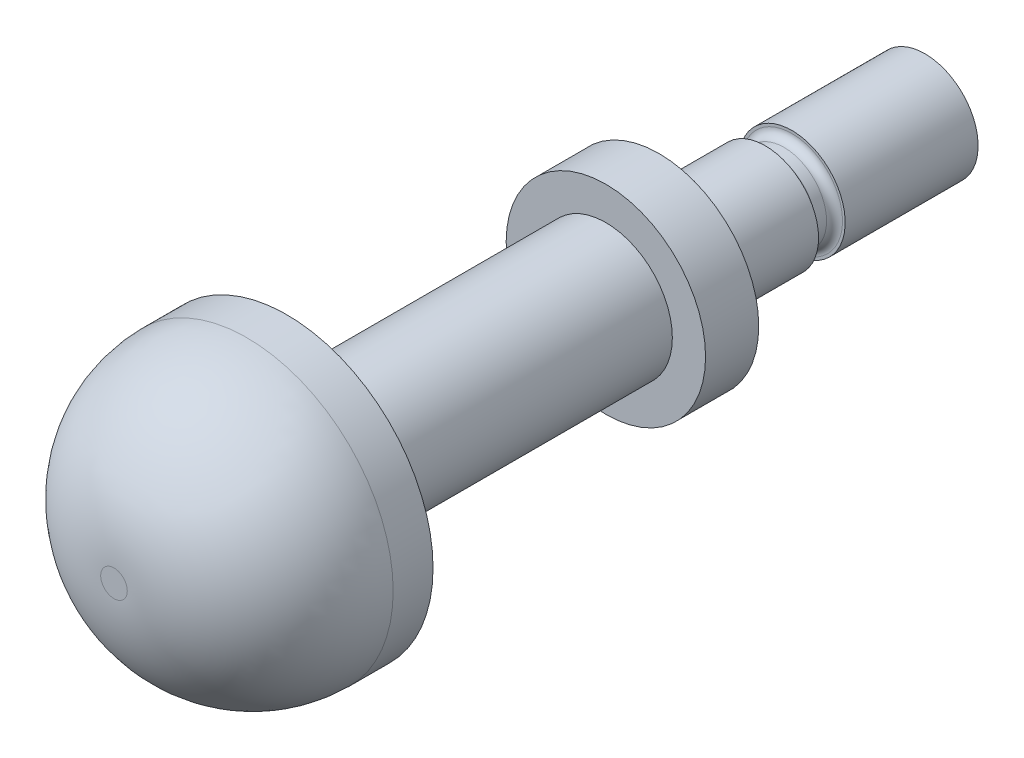
SolidWorks part; units mm, degrees
ref_plane "Plano frontal" through (0, 0, 0) normal (0, 0, 1) x (1, 0, 0)
ref_plane "Plano superior" through (0, 0, 0) normal (0, 1, 0) x (1, 0, 0)
ref_plane "Plano direito" through (0, 0, 0) normal (1, 0, 0) x (0, 0, -1)
sketch "Sketch1" plane through (0, 0, 0) normal (0, 0, 1) x (1, 0, 0)
  circle A0 centre (0, 0) radius 2
  dimension "D1" = 4
extrude "Boss-Extrude1" add sketch "Sketch1" along normal blind 4
sketch "Sketch2" plane through (0, 0, 4) normal (0, 0, 1) x (1, 0, 0)
  circle A0 centre (0, 0) radius 3.75
  dimension "D1" = 7.5
extrude "Boss-Extrude2" add sketch "Sketch2" along normal blind 2
sketch "Sketch3" plane through (0, 0, 6) normal (0, 0, 1) x (1, 0, 0)
  circle A0 centre (0, 0) radius 2.5
  dimension "D1" = 5
extrude "Boss-Extrude3" add sketch "Sketch3" along normal blind 12
sketch "Sketch4" plane through (0, 0, 18) normal (0, 0, 1) x (1, 0, 0)
  circle A0 centre (0, 0) radius 5.5
  dimension "D1" = 11
extrude "Boss-Extrude4" add sketch "Sketch4" along normal blind 6.5
fillet "Fillet1" radius 5 1 edges at (5.5, 0, 24.5)
sketch "Sketch5" plane through (0, 0, 0) normal (0, 0, -1) x (-1, 0, 0)
  circle A0 centre (0, 0) radius 1.6
  dimension "D1" = 3.2
extrude "Boss-Extrude5" add sketch "Sketch5" along normal blind 1
sketch "Sketch6" plane through (0, 0, -1) normal (0, 0, -1) x (-1, 0, 0)
  circle A0 centre (0, 0) radius 2
  dimension "D1" = 4
extrude "Boss-Extrude6" add sketch "Sketch6" along normal blind 5
fillet "Fillet2" radius 0.3 2 edges at (-1.6, 0, 0) (-1.6, 0, -1)
